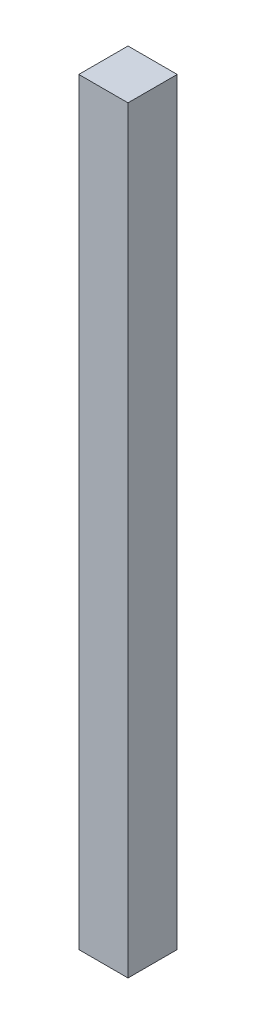
SolidWorks part; units mm, degrees
ref_plane "Front Plane" through (0, 0, 0) normal (0, 0, 1) x (1, 0, 0)
ref_plane "Top Plane" through (0, 0, 0) normal (0, 1, 0) x (1, 0, 0)
ref_plane "Right Plane" through (0, 0, 0) normal (1, 0, 0) x (0, 0, -1)
sketch "Sketch1" plane through (0, 0, 0) normal (0, 1, 0) x (1, 0, 0)
  line L1 (25, -25) -> (-25, -25)
  line L2 (25, -25) -> (25, 25)
  line L3 (25, 25) -> (-25, 25)
  line L4 (-25, -25) -> (-25, 25)
  line L5 (25, -25) -> (-25, 25) construction
  line L6 (25, 25) -> (-25, -25) construction
  point P0 (0, 0)
  dimension "D1" = 50
  dimension "D2" = 50
extrude "Boss-Extrude1" add sketch "Sketch1" along normal blind 770
